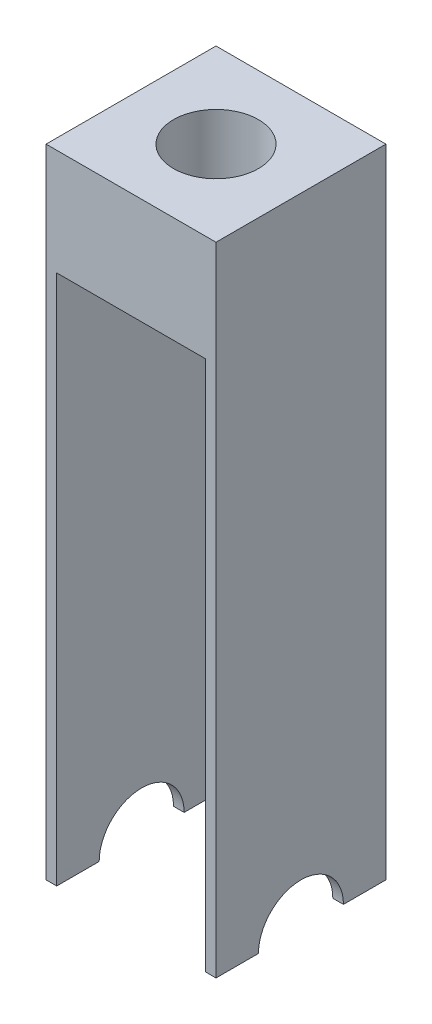
SolidWorks part; units mm, degrees
ref_plane "Front Plane" through (0, 0, 0) normal (0, 0, 1) x (1, 0, 0)
ref_plane "Top Plane" through (0, 0, 0) normal (0, 1, 0) x (1, 0, 0)
ref_plane "Right Plane" through (0, 0, 0) normal (1, 0, 0) x (0, 0, -1)
sketch "Sketch1" plane through (0, 0, 0) normal (1, 0, 0) x (0, 0, -1)
  line L0 (-20, -150) -> (-40, -150)
  line L1 (40, -150) -> (20, -150)
  line L2 (40, -150) -> (40, 150)
  line L3 (40, 150) -> (-40, 150)
  line L4 (-40, -150) -> (-40, 150)
  line L5 (40, -150) -> (-40, 150) construction
  line L6 (40, 150) -> (-40, -150) construction
  arc A0 (20, -150) -> (-20, -150) centre (0, -150) ccw
  point P0 (0, 0)
  dimension "D1" = 80
  dimension "D2" = 300
sketch "Sketch2" plane through (0, 0, 0) normal (1, 0, 0) x (0, 0, -1)
extrude "Boss-Extrude2" add sketch "Sketch1" along normal blind 80
sketch "Sketch4" plane through (0, 0, 40) normal (0, 0, 1) x (1, 0, 0)
  line L0 (80, -150) -> (0, -150) construction
  line L1 (5, 100) -> (75, 100)
  line L2 (5, 100) -> (5, -150)
  line L3 (5, -150) -> (75, -150)
  line L4 (75, 100) -> (75, -150)
  line L6 (0, 150) -> (0, -150) construction
  dimension "D1" = 70
  dimension "D2" = 5
  dimension "D3" = 250
extrude "Cut-Extrude1" cut sketch "Sketch4" against normal through all
sketch "Sketch5" plane through (0, 150, 0) normal (0, 1, 0) x (1, 0, 0)
  line L0 (80, 40) -> (0, 40) construction
  line L1 (0, 40) -> (0, -40) construction
  circle A0 centre (40, 0) radius 20
  dimension "D1" = 40
  dimension "D2" = 40
  dimension "D3" = 40
extrude "Cut-Extrude2" cut sketch "Sketch5" against normal blind 40
